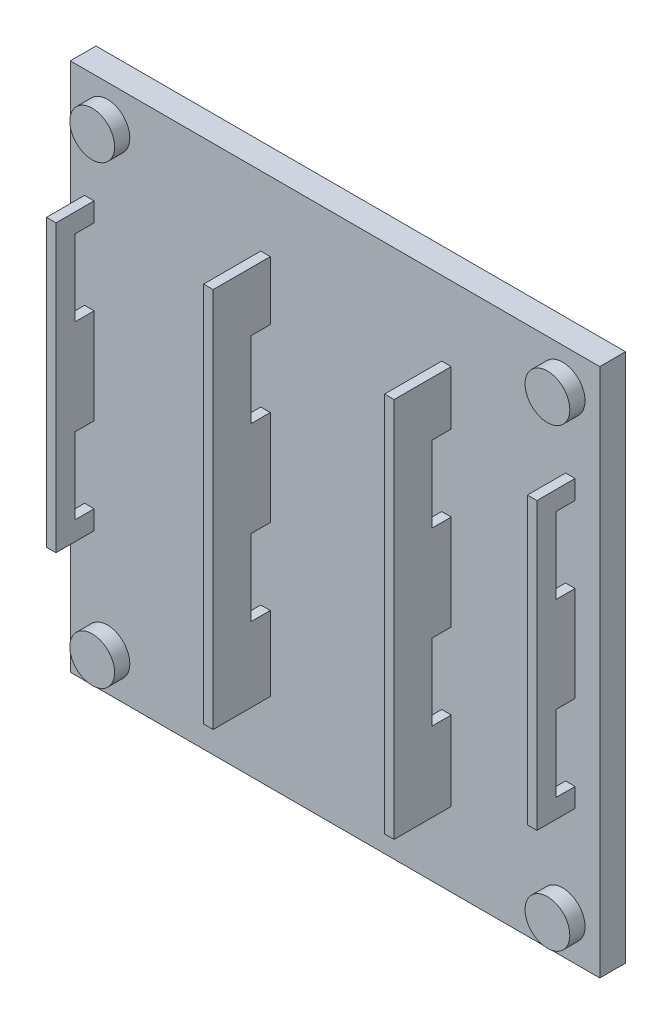
SolidWorks part; units mm, degrees
ref_plane "Přední rovina" through (0, 0, 0) normal (0, 0, 1) x (1, 0, 0)
ref_plane "Horní rovina" through (0, 0, 0) normal (0, 1, 0) x (1, 0, 0)
ref_plane "Pravá rovina" through (0, 0, 0) normal (1, 0, 0) x (0, 0, -1)
sketch "Skica1" plane through (0, 0, 0) normal (0, 0, 1) x (1, 0, 0)
  line L1 (-27.8, 27.8) -> (27.8, 27.8)
  line L2 (-27.8, 27.8) -> (-27.8, -27.8)
  line L3 (-27.8, -27.8) -> (27.8, -27.8)
  line L4 (27.8, 27.8) -> (27.8, -27.8)
  line L5 (-27.8, 27.8) -> (27.8, -27.8) construction
  line L6 (-27.8, -27.8) -> (27.8, 27.8) construction
  circle A0 centre (-23.9, 23.9) radius 2.4
  circle A1 centre (23.9, 23.9) radius 2.4
  circle A2 centre (-23.9, -23.9) radius 2.4
  circle A3 centre (23.9, -23.9) radius 2.4
  point P0 (0, 0)
  dimension "D2" = 4.8
  dimension "D6" = 4.8
  dimension "D9" = 4.8
  dimension "D11" = 4.8
  dimension "D1" = 55.6
  dimension "D3" = 3.9
  dimension "D4" = 3.9
  dimension "D5" = 5.5154
  dimension "D7" = 3.9
  dimension "D8" = 3.9
  dimension "D10" = 3.9
  dimension "D12" = 55.6
  dimension "D13" = 3.9
  dimension "D14" = 3.9
  dimension "D15" = 3.9
extrude "Přidat vysunutím1" add sketch "Skica1" along normal blind 1.9
sketch "Skica2" plane through (0, 0, 1.9) normal (0, 0, 1) x (1, 0, 0)
  line L1 (-27.8, 27.8) -> (27.8, 27.8)
  line L2 (-27.8, 27.8) -> (-27.8, -27.8)
  line L3 (-27.8, -27.8) -> (27.8, -27.8)
  line L4 (27.8, 27.8) -> (27.8, -27.8)
  line L5 (-27.8, 27.8) -> (27.8, -27.8) construction
  line L6 (-27.8, -27.8) -> (27.8, 27.8) construction
  point P0 (0, 0)
  dimension "D1" = 55.6
extrude "Přidat vysunutím2" add sketch "Skica2" along normal blind 0.8
sketch "Skica3" plane through (0, 0, 2.7) normal (0, 0, 1) x (1, 0, 0)
  line L0 (-27.8, 27.8) -> (-27.8, -27.8) construction
  line L1 (27.8, 27.8) -> (-27.8, 27.8) construction
  line L2 (27.8, -27.8) -> (27.8, 27.8) construction
  line L3 (-27.8, -27.8) -> (27.8, -27.8) construction
  circle A0 centre (-23.9, 23.9) radius 2.35
  circle A1 centre (23.9, 23.9) radius 2.35
  circle A2 centre (-23.9, -23.9) radius 2.35
  circle A3 centre (23.9, -23.9) radius 2.35
  dimension "D1" = 4.7
  dimension "D4" = 4.7
  dimension "D6" = 4.7
  dimension "D8" = 4.7
  dimension "D2" = 3.9
  dimension "D3" = 3.9
  dimension "D5" = 3.9
  dimension "D7" = 3.9
  dimension "D9" = 3.9
  dimension "D10" = 3.9
  dimension "D11" = 3.9
  dimension "D12" = 3.9
extrude "Přidat vysunutím3" add sketch "Skica3" along normal blind 1.6
sketch "Skica12" plane through (0, 0, 2.7) normal (0, 0, 1) x (1, 0, 0)
  line L0 (-27.8, 27.8) -> (-27.8, -27.8) construction
  line L1 (-7.8, 20.5) -> (-6.8, 20.5)
  line L2 (-7.8, 20.5) -> (-7.8, -19.5)
  line L3 (-7.8, -19.5) -> (-6.8, -19.5)
  line L4 (-6.8, 20.5) -> (-6.8, -19.5)
  line L5 (11.2, 20) -> (12.2, 20)
  line L6 (11.2, 20) -> (11.2, -20)
  line L7 (11.2, -20) -> (12.2, -20)
  line L8 (12.2, 20) -> (12.2, -20)
  line L9 (27.8, -27.8) -> (27.8, 27.8) construction
  line L10 (27.8, 27.8) -> (-27.8, 27.8) construction
  line L11 (-27.8, -27.8) -> (27.8, -27.8) construction
  dimension "D1" = 40
  dimension "D2" = 1
  dimension "D3" = 1
  dimension "D4" = 18
  dimension "D5" = 20
  dimension "D6" = 15.6
  dimension "D7" = 7.3
  dimension "D8" = 8.3
extrude "Přidat vysunutím5" add sketch "Skica12" along normal blind 6
sketch "Skica13" plane through (0, 0, 2.7) normal (0, 0, 1) x (1, 0, 0)
  line L0 (-7.8, 20.5) -> (-7.8, -19.5) construction
  line L1 (-26.3, 16.3198) -> (-25.3, 16.3198)
  line L2 (-26.3, 16.3198) -> (-26.3, -13.6802)
  line L3 (-26.3, -13.6802) -> (-25.3, -13.6802)
  line L4 (-25.3, 16.3198) -> (-25.3, -13.6802)
  line L5 (25.2, 16.3198) -> (24.2, 16.3198)
  line L6 (25.2, 16.3198) -> (25.2, -13.6802)
  line L7 (25.2, -13.6802) -> (24.2, -13.6802)
  line L8 (24.2, 16.3198) -> (24.2, -13.6802)
  line L9 (12.2, -20) -> (12.2, 20) construction
  dimension "D1" = 30
  dimension "D2" = 1
  dimension "D3" = 30
  dimension "D4" = 1
  dimension "D5" = 17.5
  dimension "D6" = 12
extrude "Přidat vysunutím6" add sketch "Skica13" along normal blind 4
sketch "Skica14" plane through (-26.3, 0, 0) normal (-1, 0, 0) x (0, 0, 1)
  line L0 (2.7, 16.3198) -> (2.7, -13.6802) construction
  line L1 (2.7, 14.3198) -> (4.7, 14.3198)
  line L2 (2.7, 14.3198) -> (2.7, 6.3198)
  line L3 (2.7, 6.3198) -> (4.7, 6.3198)
  line L4 (4.7, 14.3198) -> (4.7, 6.3198)
  line L5 (6.7, 16.3198) -> (2.7, 16.3198) construction
  line L6 (2.7, -3.6802) -> (4.7, -3.6802)
  line L7 (2.7, -3.6802) -> (2.7, -11.6802)
  line L8 (2.7, -11.6802) -> (4.7, -11.6802)
  line L9 (4.7, -3.6802) -> (4.7, -11.6802)
  line L10 (6.7, -13.6802) -> (2.7, -13.6802) construction
  dimension "D1" = 8
  dimension "D2" = 2
  dimension "D3" = 8
  dimension "D4" = 2
  dimension "D5" = 2
  dimension "D6" = 2
extrude "Odebrat vysunutím6" cut sketch "Skica14" against normal blind 54
sketch "Skica17" plane through (0, 0, 0) normal (0, 0, -1) x (-1, 0, 0)
  line L1 (-21, 26.5) -> (21, 26.5)
  line L2 (-21, 26.5) -> (-21, -26.5)
  line L3 (-21, -26.5) -> (21, -26.5)
  line L4 (21, 26.5) -> (21, -26.5)
  line L5 (-21, 26.5) -> (21, -26.5) construction
  line L6 (-21, -26.5) -> (21, 26.5) construction
  line L7 (-26.5, 21) -> (26.5, 21)
  line L8 (-26.5, 21) -> (-26.5, -21)
  line L9 (-26.5, -21) -> (26.5, -21)
  line L10 (26.5, 21) -> (26.5, -21)
  line L11 (-26.5, 21) -> (26.5, -21) construction
  line L12 (-26.5, -21) -> (26.5, 21) construction
  point P0 (0, 0)
  point P5 (0, 0)
  dimension "D1" = 53
  dimension "D2" = 42
  dimension "D3" = 42
  dimension "D4" = 53
extrude "Odebrat vysunutím7" cut sketch "Skica17" against normal blind 1.9 contours L8 L9 L2 L7 | L2 L7 L4 L1 | L2 L9 L4 L7 | L10 L7 L4 L9 | L9 L2 L3 L4
